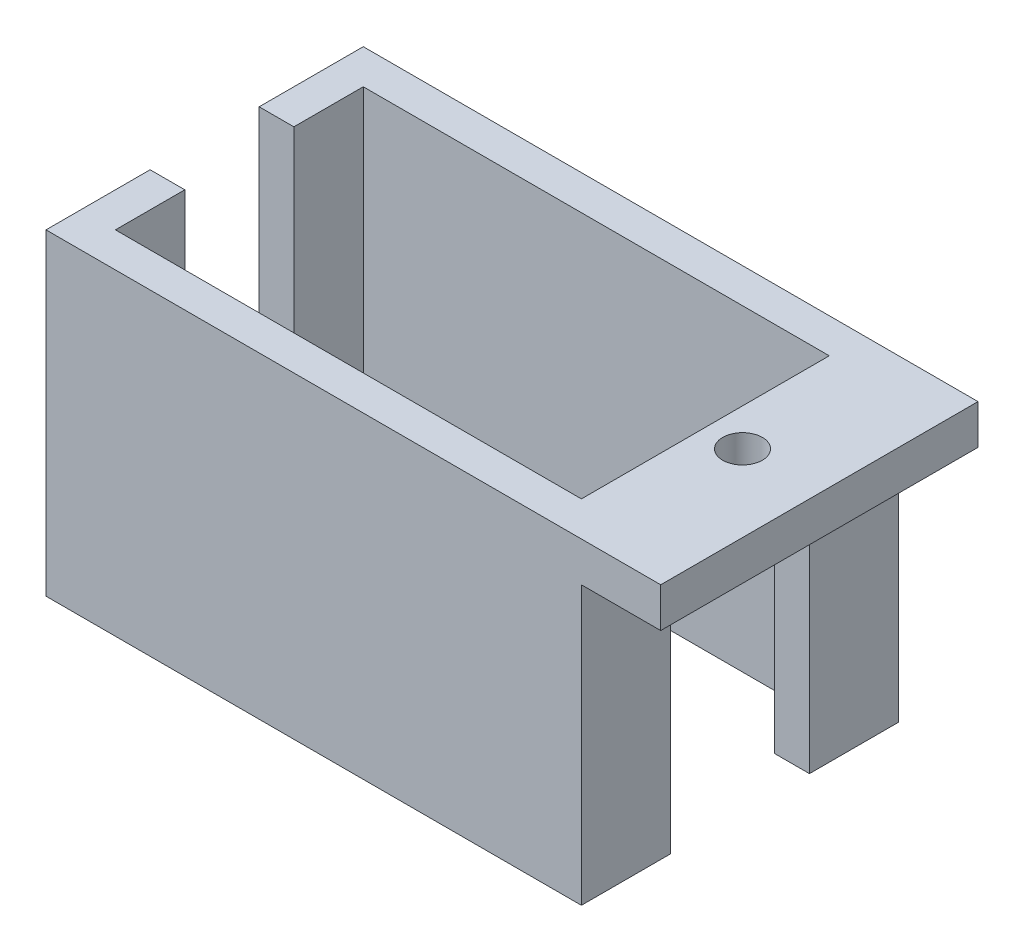
SolidWorks part; units mm, degrees
ref_plane "Front Plane" through (0, 0, 0) normal (0, 0, 1) x (1, 0, 0)
ref_plane "Top Plane" through (0, 0, 0) normal (0, 1, 0) x (1, 0, 0)
ref_plane "Right Plane" through (0, 0, 0) normal (1, 0, 0) x (0, 0, -1)
sketch "Sketch1" plane through (0, 0, 0) normal (0, 1, 0) x (1, 0, 0)
  line L1 (13.5, -8) -> (-13.5, -8)
  line L2 (13.5, -8) -> (13.5, 8)
  line L3 (13.5, 8) -> (-13.5, 8)
  line L4 (-13.5, -8) -> (-13.5, 8)
  line L5 (13.5, -8) -> (-13.5, 8) construction
  line L6 (13.5, 8) -> (-13.5, -8) construction
  point P0 (0, 0)
  dimension "D1" = 27
  dimension "D2" = 16
extrude "Boss-Extrude1" add sketch "Sketch1" along normal blind 16
sketch "Sketch2" plane through (0, 16, 0) normal (0, 1, 0) x (1, 0, 0)
  line L0 (-13.5, 8) -> (-13.5, -8) construction
  line L1 (11.75, -6.25) -> (-11.75, -6.25)
  line L2 (11.75, -6.25) -> (11.75, 6.25)
  line L3 (11.75, 6.25) -> (-11.75, 6.25)
  line L4 (-11.75, -6.25) -> (-11.75, 6.25)
  line L5 (11.75, -6.25) -> (-11.75, 6.25) construction
  line L6 (11.75, 6.25) -> (-11.75, -6.25) construction
  line L7 (-13.5, -8) -> (13.5, -8) construction
  point P0 (0, 0)
  dimension "D1" = 1.75
  dimension "D2" = 1.75
extrude "Cut-Extrude1" cut sketch "Sketch2" against normal blind 16
sketch "Sketch3" plane through (-13.5, 0, 0) normal (-1, 0, 0) x (0, 0, 1)
  line L0 (0, 0) -> (0, 27.0575) construction
  line L1 (-8, 0) -> (8, 0) construction
  line L2 (-8, 16) -> (8, 16) construction
  line L3 (-2.75, 16) -> (2.75, 16)
  line L4 (-2.75, 16) -> (-2.75, 3)
  line L5 (-2.75, 3) -> (2.75, 3)
  line L6 (2.75, 16) -> (2.75, 3)
  dimension "D1" = 13
  dimension "D2" = 5.5
extrude "Cut-Extrude2" cut sketch "Sketch3" against normal blind 4
sketch "Sketch4" plane through (13.5, 0, 0) normal (1, 0, 0) x (0, 0, -1)
  line L0 (8, 16) -> (8, 0) construction
  line L1 (-8, 16) -> (8, 16)
  line L2 (-8, 16) -> (-8, 14)
  line L3 (-8, 14) -> (8, 14)
  line L4 (8, 16) -> (8, 14)
  dimension "D1" = 2
extrude "Boss-Extrude2" add sketch "Sketch4" along normal blind 4
sketch "Sketch5" plane through (0, 16, 0) normal (0, 1, 0) x (1, 0, 0)
  circle A0 centre (13.625, 0) radius 1
  dimension "D1" = 2
extrude "Cut-Extrude3" cut sketch "Sketch5" against normal through all
sketch "Sketch6" plane through (13.5, 0, 0) normal (1, 0, 0) x (0, 0, -1)
  line L0 (0.9922, 14) -> (8, 14) construction
  line L1 (3.5, 14) -> (-3.5, 14)
  line L2 (3.5, 14) -> (3.5, 0)
  line L3 (3.5, 0) -> (-3.5, 0)
  line L4 (-3.5, 14) -> (-3.5, 0)
  line L5 (-8, 0) -> (-0.9922, 0) construction
  line L6 (0, 0) -> (0, 18.5981) construction
  line L7 (8, 14) -> (8, 0) construction
  line L8 (-8, 14) -> (-8, 0) construction
  point P10 (0, 0)
  point P11 (0, 0)
  dimension "D1" = 7
extrude "Cut-Extrude4" cut sketch "Sketch6" against normal blind 4
